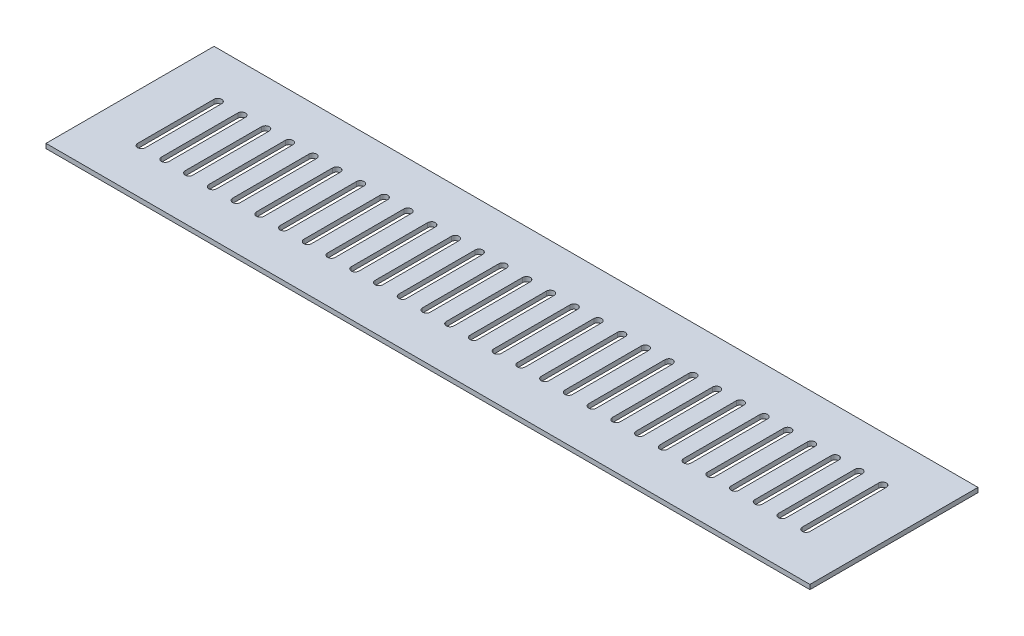
SolidWorks part; units mm, degrees
ref_plane "Ön Düzlem" through (0, 0, 0) normal (0, 0, 1) x (1, 0, 0)
ref_plane "Üst Düzlem" through (0, 0, 0) normal (0, 1, 0) x (1, 0, 0)
ref_plane "Sağ Düzlem" through (0, 0, 0) normal (1, 0, 0) x (0, 0, -1)
sketch "Çizim1" plane through (0, 0, 0) normal (0, 1, 0) x (1, 0, 0)
  line L1 (0, 0) -> (500, 0)
  line L2 (0, 0) -> (0, -110)
  line L3 (0, -110) -> (500, -110)
  line L4 (500, 0) -> (500, -110)
  dimension "D1" = 500
  dimension "D2" = 110
extrude "Yükseklik-Ekstrüzyon1" add sketch "Çizim1" along normal blind 3
sketch "Çizim2" plane through (0, 3, 0) normal (0, 1, 0) x (1, 0, 0)
  line L0 (32.5, -30) -> (32.5, -80) construction
  line L1 (35, -30) -> (35, -80)
  line L2 (30, -30) -> (30, -80)
  line L3 (0, 0) -> (0, -110) construction
  line L4 (45.5357, -30) -> (45.5357, -80)
  line L5 (50.5357, -30) -> (50.5357, -80)
  line L6 (48.0357, -30) -> (48.0357, -80) construction
  line L7 (61.0714, -30) -> (61.0714, -80)
  line L8 (66.0714, -30) -> (66.0714, -80)
  line L9 (63.5714, -30) -> (63.5714, -80) construction
  line L10 (76.6071, -30) -> (76.6071, -80)
  line L11 (81.6071, -30) -> (81.6071, -80)
  line L12 (79.1071, -30) -> (79.1071, -80) construction
  line L13 (92.1429, -30) -> (92.1429, -80)
  line L14 (97.1429, -30) -> (97.1429, -80)
  line L15 (94.6429, -30) -> (94.6429, -80) construction
  line L16 (107.6786, -30) -> (107.6786, -80)
  line L17 (112.6786, -30) -> (112.6786, -80)
  line L18 (110.1786, -30) -> (110.1786, -80) construction
  line L19 (123.2143, -30) -> (123.2143, -80)
  line L20 (128.2143, -30) -> (128.2143, -80)
  line L21 (125.7143, -30) -> (125.7143, -80) construction
  line L22 (138.75, -30) -> (138.75, -80)
  line L23 (143.75, -30) -> (143.75, -80)
  line L24 (141.25, -30) -> (141.25, -80) construction
  line L25 (154.2857, -30) -> (154.2857, -80)
  line L26 (159.2857, -30) -> (159.2857, -80)
  line L27 (156.7857, -30) -> (156.7857, -80) construction
  line L28 (169.8214, -30) -> (169.8214, -80)
  line L29 (174.8214, -30) -> (174.8214, -80)
  line L30 (172.3214, -30) -> (172.3214, -80) construction
  line L31 (185.3571, -30) -> (185.3571, -80)
  line L32 (190.3571, -30) -> (190.3571, -80)
  line L33 (187.8571, -30) -> (187.8571, -80) construction
  line L34 (200.8929, -30) -> (200.8929, -80)
  line L35 (205.8929, -30) -> (205.8929, -80)
  line L36 (203.3929, -30) -> (203.3929, -80) construction
  line L37 (216.4286, -30) -> (216.4286, -80)
  line L38 (221.4286, -30) -> (221.4286, -80)
  line L39 (218.9286, -30) -> (218.9286, -80) construction
  line L40 (231.9643, -30) -> (231.9643, -80)
  line L41 (236.9643, -30) -> (236.9643, -80)
  line L42 (234.4643, -30) -> (234.4643, -80) construction
  line L43 (247.5, -30) -> (247.5, -80)
  line L44 (252.5, -30) -> (252.5, -80)
  line L45 (250, -30) -> (250, -80) construction
  line L46 (263.0357, -30) -> (263.0357, -80)
  line L47 (268.0357, -30) -> (268.0357, -80)
  line L48 (265.5357, -30) -> (265.5357, -80) construction
  line L49 (278.5714, -30) -> (278.5714, -80)
  line L50 (283.5714, -30) -> (283.5714, -80)
  line L51 (281.0714, -30) -> (281.0714, -80) construction
  line L52 (294.1071, -30) -> (294.1071, -80)
  line L53 (299.1071, -30) -> (299.1071, -80)
  line L54 (296.6071, -30) -> (296.6071, -80) construction
  line L55 (309.6429, -30) -> (309.6429, -80)
  line L56 (314.6429, -30) -> (314.6429, -80)
  line L57 (312.1429, -30) -> (312.1429, -80) construction
  line L58 (325.1786, -30) -> (325.1786, -80)
  line L59 (330.1786, -30) -> (330.1786, -80)
  line L60 (327.6786, -30) -> (327.6786, -80) construction
  line L61 (340.7143, -30) -> (340.7143, -80)
  line L62 (345.7143, -30) -> (345.7143, -80)
  line L63 (343.2143, -30) -> (343.2143, -80) construction
  line L64 (356.25, -30) -> (356.25, -80)
  line L65 (361.25, -30) -> (361.25, -80)
  line L66 (358.75, -30) -> (358.75, -80) construction
  line L67 (371.7857, -30) -> (371.7857, -80)
  line L68 (376.7857, -30) -> (376.7857, -80)
  line L69 (374.2857, -30) -> (374.2857, -80) construction
  line L70 (387.3214, -30) -> (387.3214, -80)
  line L71 (392.3214, -30) -> (392.3214, -80)
  line L72 (389.8214, -30) -> (389.8214, -80) construction
  line L73 (402.8571, -30) -> (402.8571, -80)
  line L74 (407.8571, -30) -> (407.8571, -80)
  line L75 (405.3571, -30) -> (405.3571, -80) construction
  line L76 (418.3929, -30) -> (418.3929, -80)
  line L77 (423.3929, -30) -> (423.3929, -80)
  line L78 (420.8929, -30) -> (420.8929, -80) construction
  line L79 (433.9286, -30) -> (433.9286, -80)
  line L80 (438.9286, -30) -> (438.9286, -80)
  line L81 (436.4286, -30) -> (436.4286, -80) construction
  line L82 (449.4643, -30) -> (449.4643, -80)
  line L83 (454.4643, -30) -> (454.4643, -80)
  line L84 (451.9643, -30) -> (451.9643, -80) construction
  line L85 (465, -30) -> (465, -80)
  line L86 (470, -30) -> (470, -80)
  line L87 (467.5, -30) -> (467.5, -80) construction
  line L88 (500, -110) -> (500, 0) construction
  arc A0 (35, -30) -> (30, -30) centre (32.5, -30) ccw
  arc A1 (30, -80) -> (35, -80) centre (32.5, -80) ccw
  arc A2 (50.5357, -30) -> (45.5357, -30) centre (48.0357, -30) ccw
  arc A3 (45.5357, -80) -> (50.5357, -80) centre (48.0357, -80) ccw
  arc A4 (66.0714, -30) -> (61.0714, -30) centre (63.5714, -30) ccw
  arc A5 (61.0714, -80) -> (66.0714, -80) centre (63.5714, -80) ccw
  arc A6 (81.6071, -30) -> (76.6071, -30) centre (79.1071, -30) ccw
  arc A7 (76.6071, -80) -> (81.6071, -80) centre (79.1071, -80) ccw
  arc A8 (97.1429, -30) -> (92.1429, -30) centre (94.6429, -30) ccw
  arc A9 (92.1429, -80) -> (97.1429, -80) centre (94.6429, -80) ccw
  arc A10 (112.6786, -30) -> (107.6786, -30) centre (110.1786, -30) ccw
  arc A11 (107.6786, -80) -> (112.6786, -80) centre (110.1786, -80) ccw
  arc A12 (128.2143, -30) -> (123.2143, -30) centre (125.7143, -30) ccw
  arc A13 (123.2143, -80) -> (128.2143, -80) centre (125.7143, -80) ccw
  arc A14 (143.75, -30) -> (138.75, -30) centre (141.25, -30) ccw
  arc A15 (138.75, -80) -> (143.75, -80) centre (141.25, -80) ccw
  arc A16 (159.2857, -30) -> (154.2857, -30) centre (156.7857, -30) ccw
  arc A17 (154.2857, -80) -> (159.2857, -80) centre (156.7857, -80) ccw
  arc A18 (174.8214, -30) -> (169.8214, -30) centre (172.3214, -30) ccw
  arc A19 (169.8214, -80) -> (174.8214, -80) centre (172.3214, -80) ccw
  arc A20 (190.3571, -30) -> (185.3571, -30) centre (187.8571, -30) ccw
  arc A21 (185.3571, -80) -> (190.3571, -80) centre (187.8571, -80) ccw
  arc A22 (205.8929, -30) -> (200.8929, -30) centre (203.3929, -30) ccw
  arc A23 (200.8929, -80) -> (205.8929, -80) centre (203.3929, -80) ccw
  arc A24 (221.4286, -30) -> (216.4286, -30) centre (218.9286, -30) ccw
  arc A25 (216.4286, -80) -> (221.4286, -80) centre (218.9286, -80) ccw
  arc A26 (236.9643, -30) -> (231.9643, -30) centre (234.4643, -30) ccw
  arc A27 (231.9643, -80) -> (236.9643, -80) centre (234.4643, -80) ccw
  arc A28 (252.5, -30) -> (247.5, -30) centre (250, -30) ccw
  arc A29 (247.5, -80) -> (252.5, -80) centre (250, -80) ccw
  arc A30 (268.0357, -30) -> (263.0357, -30) centre (265.5357, -30) ccw
  arc A31 (263.0357, -80) -> (268.0357, -80) centre (265.5357, -80) ccw
  arc A32 (283.5714, -30) -> (278.5714, -30) centre (281.0714, -30) ccw
  arc A33 (278.5714, -80) -> (283.5714, -80) centre (281.0714, -80) ccw
  arc A34 (299.1071, -30) -> (294.1071, -30) centre (296.6071, -30) ccw
  arc A35 (294.1071, -80) -> (299.1071, -80) centre (296.6071, -80) ccw
  arc A36 (314.6429, -30) -> (309.6429, -30) centre (312.1429, -30) ccw
  arc A37 (309.6429, -80) -> (314.6429, -80) centre (312.1429, -80) ccw
  arc A38 (330.1786, -30) -> (325.1786, -30) centre (327.6786, -30) ccw
  arc A39 (325.1786, -80) -> (330.1786, -80) centre (327.6786, -80) ccw
  arc A40 (345.7143, -30) -> (340.7143, -30) centre (343.2143, -30) ccw
  arc A41 (340.7143, -80) -> (345.7143, -80) centre (343.2143, -80) ccw
  arc A42 (361.25, -30) -> (356.25, -30) centre (358.75, -30) ccw
  arc A43 (356.25, -80) -> (361.25, -80) centre (358.75, -80) ccw
  arc A44 (376.7857, -30) -> (371.7857, -30) centre (374.2857, -30) ccw
  arc A45 (371.7857, -80) -> (376.7857, -80) centre (374.2857, -80) ccw
  arc A46 (392.3214, -30) -> (387.3214, -30) centre (389.8214, -30) ccw
  arc A47 (387.3214, -80) -> (392.3214, -80) centre (389.8214, -80) ccw
  arc A48 (407.8571, -30) -> (402.8571, -30) centre (405.3571, -30) ccw
  arc A49 (402.8571, -80) -> (407.8571, -80) centre (405.3571, -80) ccw
  arc A50 (423.3929, -30) -> (418.3929, -30) centre (420.8929, -30) ccw
  arc A51 (418.3929, -80) -> (423.3929, -80) centre (420.8929, -80) ccw
  arc A52 (438.9286, -30) -> (433.9286, -30) centre (436.4286, -30) ccw
  arc A53 (433.9286, -80) -> (438.9286, -80) centre (436.4286, -80) ccw
  arc A54 (454.4643, -30) -> (449.4643, -30) centre (451.9643, -30) ccw
  arc A55 (449.4643, -80) -> (454.4643, -80) centre (451.9643, -80) ccw
  arc A56 (470, -30) -> (465, -30) centre (467.5, -30) ccw
  arc A57 (465, -80) -> (470, -80) centre (467.5, -80) ccw
  point P2 (32.5, -55)
  point P9 (0, -55)
  point P13 (48.0357, -55)
  point P20 (63.5714, -55)
  point P27 (79.1071, -55)
  point P34 (94.6429, -55)
  point P41 (110.1786, -55)
  point P48 (125.7143, -55)
  point P55 (141.25, -55)
  point P62 (156.7857, -55)
  point P69 (172.3214, -55)
  point P76 (187.8571, -55)
  point P83 (203.3929, -55)
  point P90 (218.9286, -55)
  point P97 (234.4643, -55)
  point P104 (250, -55)
  point P111 (265.5357, -55)
  point P118 (281.0714, -55)
  point P125 (296.6071, -55)
  point P132 (312.1429, -55)
  point P139 (327.6786, -55)
  point P146 (343.2143, -55)
  point P153 (358.75, -55)
  point P160 (374.2857, -55)
  point P167 (389.8214, -55)
  point P174 (405.3571, -55)
  point P181 (420.8929, -55)
  point P188 (436.4286, -55)
  point P195 (451.9643, -55)
  point P202 (467.5, -55)
  dimension "D1" = 50
  dimension "D2" = 30
  dimension "D3" = 5
  dimension "D5" = 30
  dimension "D4" = 29
extrude "Kes-Ekstrüzyon1" cut sketch "Çizim2" against normal blind 3
